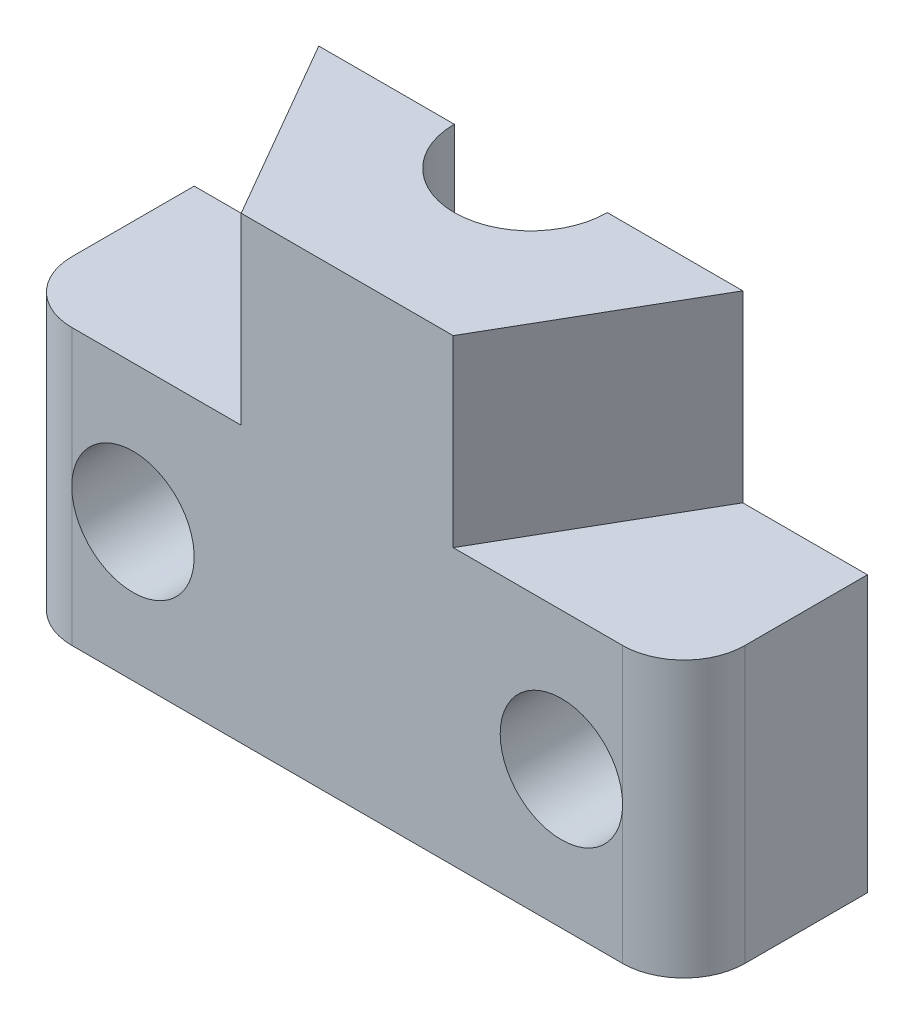
SolidWorks part; units mm, degrees
ref_plane "Спереди" through (0, 0, 0) normal (0, 0, 1) x (1, 0, 0)
ref_plane "Сверху" through (0, 0, 0) normal (0, 1, 0) x (1, 0, 0)
ref_plane "Справа" through (0, 0, 0) normal (1, 0, 0) x (0, 0, -1)
sketch "Эскиз1" plane through (0, 0, 0) normal (0, 1, 0) x (1, 0, 0)
  line L1 (-11, -6) -> (11, -6)
  line L2 (-11, -6) -> (-11, 6)
  line L3 (-11, 6) -> (11, 6)
  line L4 (11, -6) -> (11, 6)
  line L5 (-11, -6) -> (11, 6) construction
  line L6 (-11, 6) -> (11, -6) construction
  point P0 (0, 0)
  dimension "D1" = 12
  dimension "D2" = 22
extrude "Бобышка-Вытянуть1" add sketch "Эскиз1" along normal blind 9
fillet "Скругление1" radius 2 4 edges at (-11, 4.5, -6) (11, 4.5, -6) (11, 4.5, 6) (-11, 4.5, 6)
sketch "Эскиз2" plane through (0, 0, 0) normal (0, 1, 0) x (1, 0, 0)
  circle A0 centre (0, 0) radius 3.6
  dimension "D1" = 7.2
extrude "Вырез-Вытянуть1" cut sketch "Эскиз2" along normal blind 8
sketch "Эскиз3" plane through (0, 8, 0) normal (0, -1, 0) x (1, 0, 0)
  circle A0 centre (0, 0) radius 5
  dimension "D1" = 10
extrude "Вырез-Вытянуть2" cut sketch "Эскиз3" against normal mid plane 2
sketch "Эскиз6" plane through (0, 9, 0) normal (0, 1, 0) x (1, 0, 0)
  line L1 (6.9282, 0) -> (3.4641, 6)
  line L2 (3.4641, 6) -> (-3.4641, 6)
  line L3 (-3.4641, 6) -> (-6.9282, 0)
  line L4 (-6.9282, 0) -> (-3.4641, -6)
  line L5 (-3.4641, -6) -> (3.4641, -6)
  line L6 (3.4641, -6) -> (6.9282, 0)
  circle A0 centre (0, 0) radius 6 construction
extrude "Бобышка-Вытянуть2" add sketch "Эскиз6" along normal blind 6
sketch "Эскиз7" plane through (0, 9, 0) normal (0, 1, 0) x (1, 0, 0)
  line L1 (4.6188, 0) -> (2.3094, 4)
  line L2 (2.3094, 4) -> (-2.3094, 4)
  line L3 (-2.3094, 4) -> (-4.6188, 0)
  line L4 (-4.6188, 0) -> (-2.3094, -4)
  line L5 (-2.3094, -4) -> (2.3094, -4)
  line L6 (2.3094, -4) -> (4.6188, 0)
  circle A0 centre (0, 0) radius 4 construction
extrude "Вырез-Вытянуть5" cut sketch "Эскиз7" along normal blind 3
sketch "Эскиз8" plane through (0, 9, 0) normal (0, 1, 0) x (1, 0, 0)
  circle A0 centre (0, 0) radius 2.5
  dimension "D1" = 5
extrude "Вырез-Вытянуть6" cut sketch "Эскиз8" along normal up to surface (6 mm away) up to face at (0, 15, 0)
sketch "Эскиз11" plane through (0, 0, -6) normal (0, 0, -1) x (-1, 0, 0)
  line L0 (-9, 4.5) -> (9, 4.5) construction
  line L1 (-9, 9) -> (-9, 0) construction
  line L2 (9, 0) -> (9, 9) construction
  circle A0 centre (7, 4.5) radius 2
  dimension "D1" = 7
  dimension "D2" = 4
extrude "Вырез-Вытянуть9" cut sketch "Эскиз11" against normal through all
mirror "Зеркальное отражение6" about plane through (0, 0, 0) normal (1, 0, 0) of "Вырез-Вытянуть9"
sketch "Эскиз12" plane through (0, 0, 0) normal (0, 0, 1) x (1, 0, 0)
  line L1 (-13.5856, -16.6171) -> (13.5856, -16.6171)
  line L2 (-13.5856, -16.6171) -> (-13.5856, 16.6171)
  line L3 (-13.5856, 16.6171) -> (13.5856, 16.6171)
  line L4 (13.5856, -16.6171) -> (13.5856, 16.6171)
  line L5 (-13.5856, -16.6171) -> (13.5856, 16.6171) construction
  line L6 (-13.5856, 16.6171) -> (13.5856, -16.6171) construction
  point P0 (0, 0)
extrude "Вырез-Вытянуть10" cut sketch "Эскиз12" against normal blind 10
